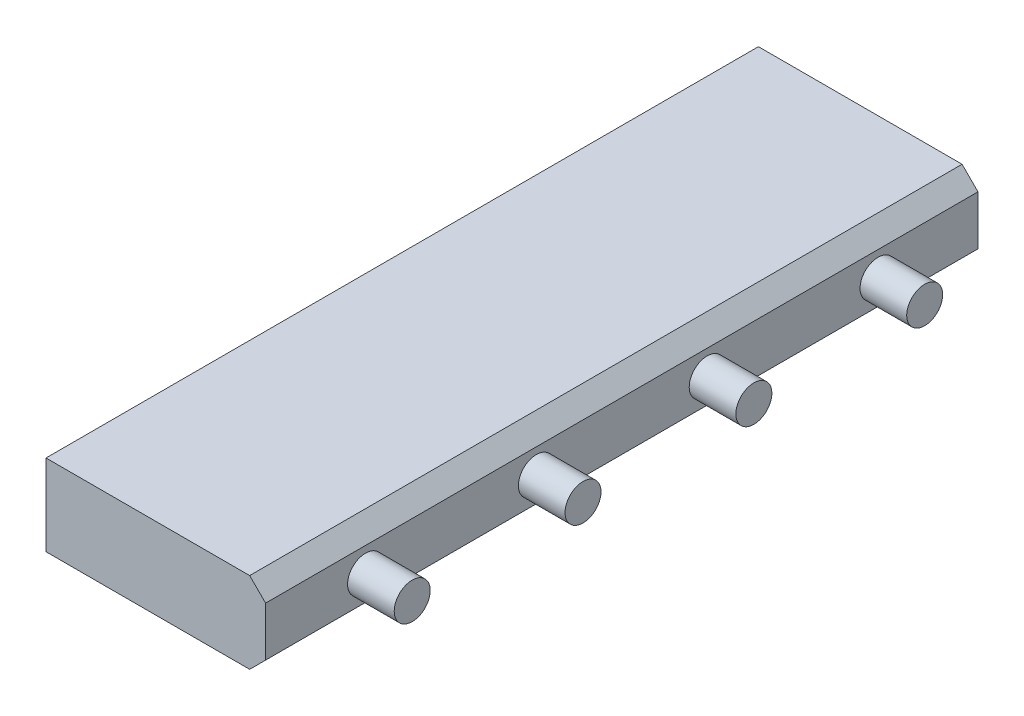
SolidWorks part; units mm, degrees
ref_plane "Top Plane" through (0, 0, 0) normal (0, 0, 1) x (1, 0, 0)
ref_plane "Front Plane" through (0, 0, 0) normal (0, 1, 0) x (1, 0, 0)
ref_plane "Right Plane" through (0, 0, 0) normal (1, 0, 0) x (0, 0, -1)
sketch "Sketch1" plane through (0, 0, 0) normal (0, 0, 1) x (1, 0, 0)
  line L0 (0, 0) -> (0.6112, 0)
  line L1 (0.4133, 0) -> (-0.4133, 0) construction
  line L3 (0.659, 0.196) -> (0.659, 0.0478)
  line L6 (0, -0.1341) -> (0, 0.1341) construction
  line L7 (0, 0.2438) -> (0, 0)
  line L8 (0.6112, 0) -> (0.659, 0.0478)
  line L9 (0, 0.2438) -> (0.6112, 0.2438)
  line L10 (0.6112, 0.2438) -> (0.659, 0.196)
  dimension "D1" = 0.659
  dimension "D2" = 45
  dimension "D3" = 0.0478
  dimension "D4" = 0.2437
  dimension "D5" = 45
extrude "Boss-Extrude1" add sketch "Sketch1" along normal blind 2.138
sketch "Sketch2" plane through (0.659, 0, 0) normal (1, 0, 0) x (0, 0, -1)
  line L0 (0, 0.1219) -> (-0.3, 0.1219) construction
  line L1 (0, 0.0478) -> (0, 0.196) construction
  line L2 (-0.3, 0.1219) -> (-0.3, 0.5596) construction
  line L3 (-0.3, 0.1219) -> (-0.8127, 0.1219) construction
  line L4 (-0.8127, 0.1219) -> (-1.3253, 0.1219) construction
  line L5 (-1.3253, 0.1219) -> (-1.838, 0.1219) construction
  line L6 (-1.838, 0.1219) -> (-1.838, 0.4104) construction
  line L7 (-1.3253, 0.1219) -> (-1.3253, 0.4104) construction
  line L8 (-0.8127, 0.1219) -> (-0.8127, 0.4257) construction
  line L9 (-1.838, 0.1219) -> (-2.138, 0.1219) construction
  line L10 (-2.138, 0.0478) -> (-2.138, 0.196) construction
  circle A0 centre (-1.838, 0.1219) radius 0.054
  circle A1 centre (-1.3253, 0.1219) radius 0.054
  circle A2 centre (-0.8127, 0.1219) radius 0.054
  circle A3 centre (-0.3, 0.1219) radius 0.054
  dimension "D1" = 0.3
extrude "Boss-Extrude2" add sketch "Sketch2" along normal blind 0.14
